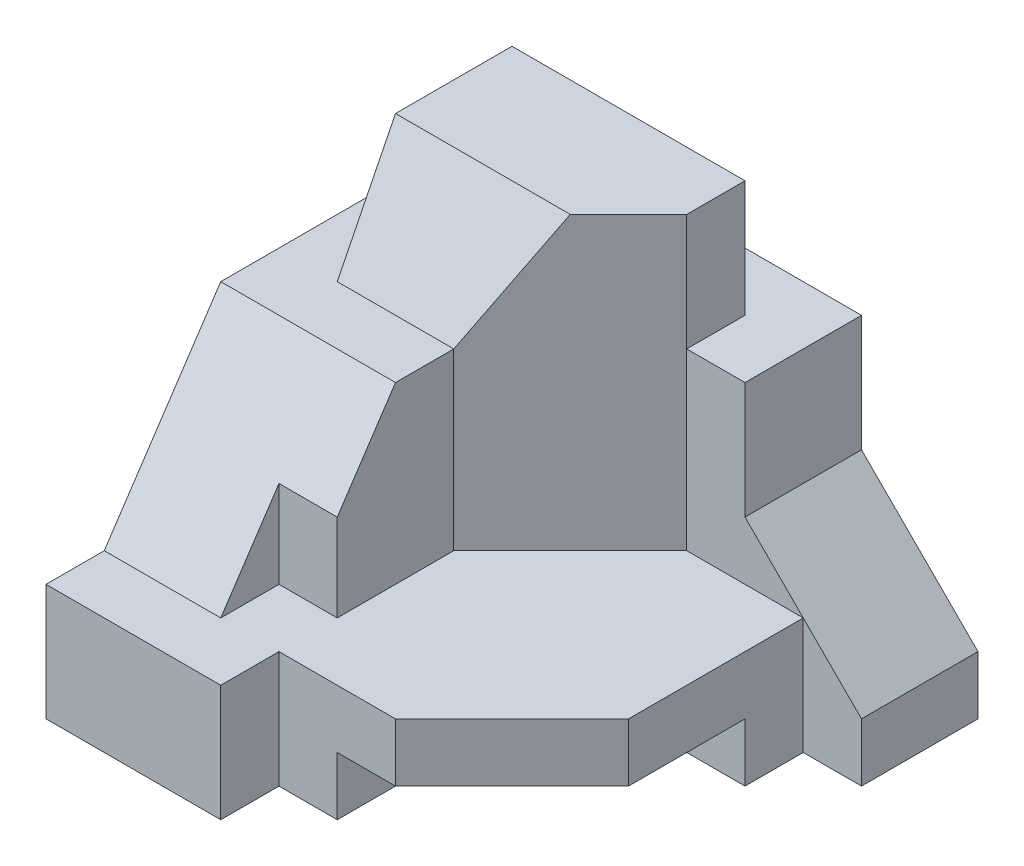
SolidWorks part; units mm, degrees
ref_plane "Front Plane" through (0, 0, 0) normal (0, 0, 1) x (1, 0, 0)
ref_plane "Top Plane" through (0, 0, 0) normal (0, 1, 0) x (1, 0, 0)
ref_plane "Right Plane" through (0, 0, 0) normal (1, 0, 0) x (0, 0, -1)
sketch "Sketch1" plane through (0, 0, 0) normal (0, 0, 1) x (1, 0, 0)
  line L1 (4, -3.5) -> (-4, -3.5)
  line L2 (4, -3.5) -> (4, 3.5)
  line L3 (4, 3.5) -> (-4, 3.5)
  line L4 (-4, -3.5) -> (-4, 3.5)
  line L5 (4, -3.5) -> (-4, 3.5) construction
  line L6 (4, 3.5) -> (-4, -3.5) construction
  point P0 (0, 0)
  dimension "D1" = 8
  dimension "D2" = 7
extrude "Boss-Extrude3" add sketch "Sketch1" along normal blind 8
sketch "Sketch3" plane through (0, 3.5, 0) normal (0, 1, 0) x (1, 0, 0)
  line L0 (4, -8) -> (4, -2)
  line L1 (4, -8) -> (4, 0) construction
  line L2 (4, -2) -> (3, -2)
  line L3 (3, -2) -> (3, -5)
  line L4 (3, -5) -> (1, -7)
  line L5 (1, -7) -> (-1, -7)
  line L6 (-1, -7) -> (-1, -8)
  line L7 (4, -8) -> (-4, -8) construction
  line L8 (-1, -8) -> (4, -8)
  dimension "D1" = 3
  dimension "D2" = 2
  dimension "D3" = 3
  dimension "D4" = 1
  dimension "D5" = 1
  dimension "D6" = 2
extrude "Cut-Extrude1" cut sketch "Sketch3" against normal through all
sketch "Sketch4" plane through (0, -3.5, 0) normal (0, -1, 0) x (1, 0, 0)
  line L0 (1, 7) -> (3, 5)
  line L1 (3, 5) -> (3, 3)
  line L2 (3, 2) -> (3, 5) construction
  line L3 (3, 3) -> (0, 3)
  line L4 (0, 3) -> (0, 7)
  line L5 (1, 7) -> (-1, 7) construction
  line L6 (0, 7) -> (1, 7)
  dimension "D1" = 1
  dimension "D2" = 1
extrude "Cut-Extrude2" cut sketch "Sketch4" against normal blind 1
sketch "Sketch5" plane through (0, 0, 0) normal (0, 0, -1) x (-1, 0, 0)
  line L0 (-2, -0.5) -> (-2, 1.5)
  line L2 (-2, 1.5) -> (-2, 3.5)
  line L3 (-2, -0.5) -> (-4, -2.5)
  line L4 (-4, -3.5) -> (-4, 3.5) construction
  line L5 (-4, 1.5) -> (-4, -2.5)
  line L7 (-4, 3.5) -> (4, 3.5) construction
  line L8 (-2, 3.5) -> (-4, 3.5)
  line L9 (-4, 3.5) -> (-4, 1.5)
  dimension "D1" = 2
  dimension "D2" = 2
  dimension "D3" = 1
  dimension "D4" = 2
  dimension "D5" = 2.8284
extrude "Cut-Extrude4" cut sketch "Sketch5" against normal blind 2
sketch "Sketch6" plane through (-4, 0, 0) normal (-1, 0, 0) x (0, 0, 1)
  line L0 (8, -1.5) -> (7, -1.5)
  line L1 (8, 3.5) -> (8, -3.5) construction
  line L2 (7, -1.5) -> (5, 1.5)
  line L3 (5, 1.5) -> (5, 3.5)
  line L4 (8, 3.5) -> (0, 3.5) construction
  line L5 (5, 3.5) -> (8, 3.5)
  line L6 (8, 3.5) -> (8, -1.5)
  dimension "D1" = 2
  dimension "D2" = 1
  dimension "D3" = 2
  dimension "D4" = 3
extrude "Cut-Extrude5" cut sketch "Sketch6" against normal through all
sketch "Sketch7" plane through (0, 3.5, 0) normal (0, 1, 0) x (1, 0, 0)
  line L0 (-3, -1) -> (-3, -4)
  line L1 (-3, -4) -> (1, -4)
  line L2 (1, -4) -> (1, -1)
  line L3 (1, -1) -> (-3, -1)
  line L4 (2, -2) -> (2, 0) construction
  line L5 (-4, -5) -> (-4, 0) construction
  line L6 (2, 0) -> (-4, 0) construction
  dimension "D1" = 1
  dimension "D2" = 1
  dimension "D3" = 1
  dimension "D4" = 3
extrude "Cut-Extrude6" cut sketch "Sketch7" against normal blind 2 flip side to cut
sketch "Sketch8" plane through (0, 1.5, 0) normal (0, 1, 0) x (1, 0, 0)
  line L0 (-1, -7) -> (-1, -6)
  line L1 (-1, -6) -> (-2, -6)
  line L2 (-2, -6) -> (-2, -7)
  line L3 (-2, -7) -> (-1, -7)
  line L4 (-4, -5) -> (-4, -7) construction
  line L5 (-1, -7) -> (-4, -7) construction
  dimension "D1" = 1
  dimension "D2" = 1
  dimension "D3" = 2
  dimension "D4" = 1
extrude "Cut-Extrude7" cut sketch "Sketch8" against normal blind 3
sketch "Sketch9" plane through (0, 3.5, 0) normal (0, 1, 0) x (1, 0, 0)
  line L0 (-1, -6) -> (-1, -4)
  line L1 (-3, -4) -> (1, -4) construction
  line L2 (-1, -4) -> (3, -4)
  line L3 (3, -5) -> (3, -2) construction
  line L4 (3, -4) -> (3, -7)
  line L5 (3, -7) -> (-1, -7)
  line L6 (-1, -7) -> (-1, -8) construction
  line L7 (-1, -7) -> (-1, -6)
  line L9 (1, -7) -> (-1, -7) construction
extrude "Cut-Extrude8" cut sketch "Sketch9" against normal blind 5
sketch "Sketch10" plane through (0, 3.5, 0) normal (0, 1, 0) x (1, 0, 0)
  line L0 (-3, -3) -> (1, -3)
  line L1 (-3, -1) -> (-3, -4) construction
  line L2 (1, -4) -> (1, -1) construction
  dimension "D1" = 1
ref_plane "Plane1" through (0, 1.9, 3.8) normal (0, 0.4472, 0.8944) x (1, 0, 0)
sketch "Sketch11" plane through (0, 1.9, 3.8) normal (0, 0.4472, 0.8944) x (1, 0, 0)
  line L0 (-3, 1.7889) -> (1, 1.7889)
  line L1 (1, 1.7889) -> (1, -0.4472)
  line L2 (1, -0.4472) -> (-3, -0.4472)
  line L3 (-3, -0.4472) -> (-3, 1.7889)
extrude "Cut-Extrude9" cut sketch "Sketch11" along normal blind 5
sketch "Sketch12" plane through (0, 3.5, 0) normal (0, 1, 0) x (1, 0, 0)
  line L0 (1, -2) -> (-1, -4)
  line L1 (1, -3) -> (1, -1) construction
  line L2 (-1, -4) -> (1, -4)
  line L3 (3, -4) -> (-1, -4) construction
  line L4 (1, -4) -> (1, -2)
extrude "Cut-Extrude10" cut sketch "Sketch12" against normal blind 5
sketch "Sketch13" plane through (0, 1.5, 0) normal (0, 1, 0) x (1, 0, 0)
  line L0 (1, -2) -> (3, -2)
  line L1 (3, -2) -> (3, -4)
  line L2 (3, -4) -> (1, -4)
  line L3 (1, -4) -> (1, -2)
extrude "Cut-Extrude12" cut sketch "Sketch13" against normal blind 3
